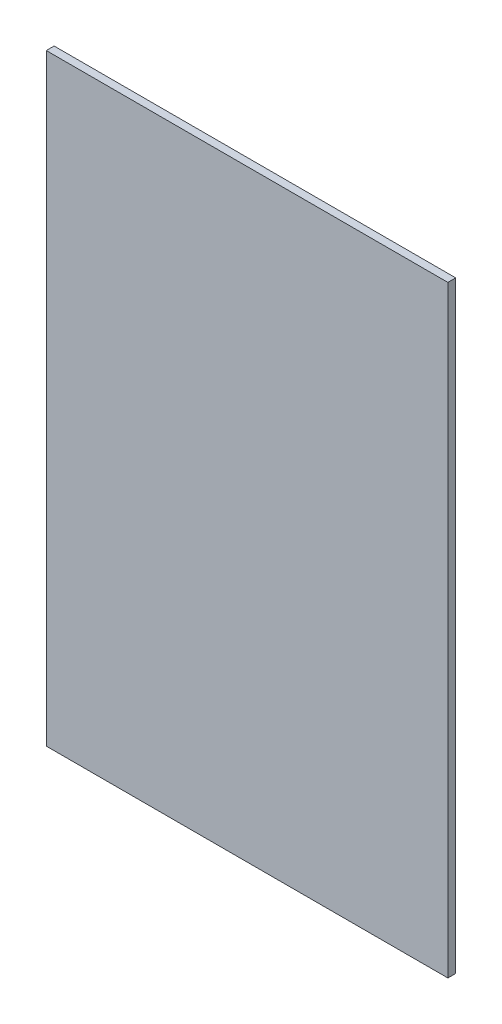
SolidWorks part; units mm, degrees
material "Cedar"
ref_plane "Front Plane" through (0, 0, 0) normal (0, 0, 1) x (1, 0, 0)
ref_plane "Top Plane" through (0, 0, 0) normal (0, 1, 0) x (1, 0, 0)
ref_plane "Right Plane" through (0, 0, 0) normal (1, 0, 0) x (0, 0, -1)
sketch "Sketch1" plane through (0, 0, 0) normal (0, 0, 1) x (1, 0, 0)
  line L1 (-304.8, -457.2) -> (304.8, -457.2)
  line L2 (-304.8, -457.2) -> (-304.8, 457.2)
  line L3 (-304.8, 457.2) -> (304.8, 457.2)
  line L4 (304.8, -457.2) -> (304.8, 457.2)
  line L5 (-304.8, -457.2) -> (304.8, 457.2) construction
  line L6 (-304.8, 457.2) -> (304.8, -457.2) construction
  point P0 (0, 0)
  dimension "D1" = 609.6
  dimension "D2" = 914.4
extrude "Boss-Extrude1" add sketch "Sketch1" along normal blind 11.9062
